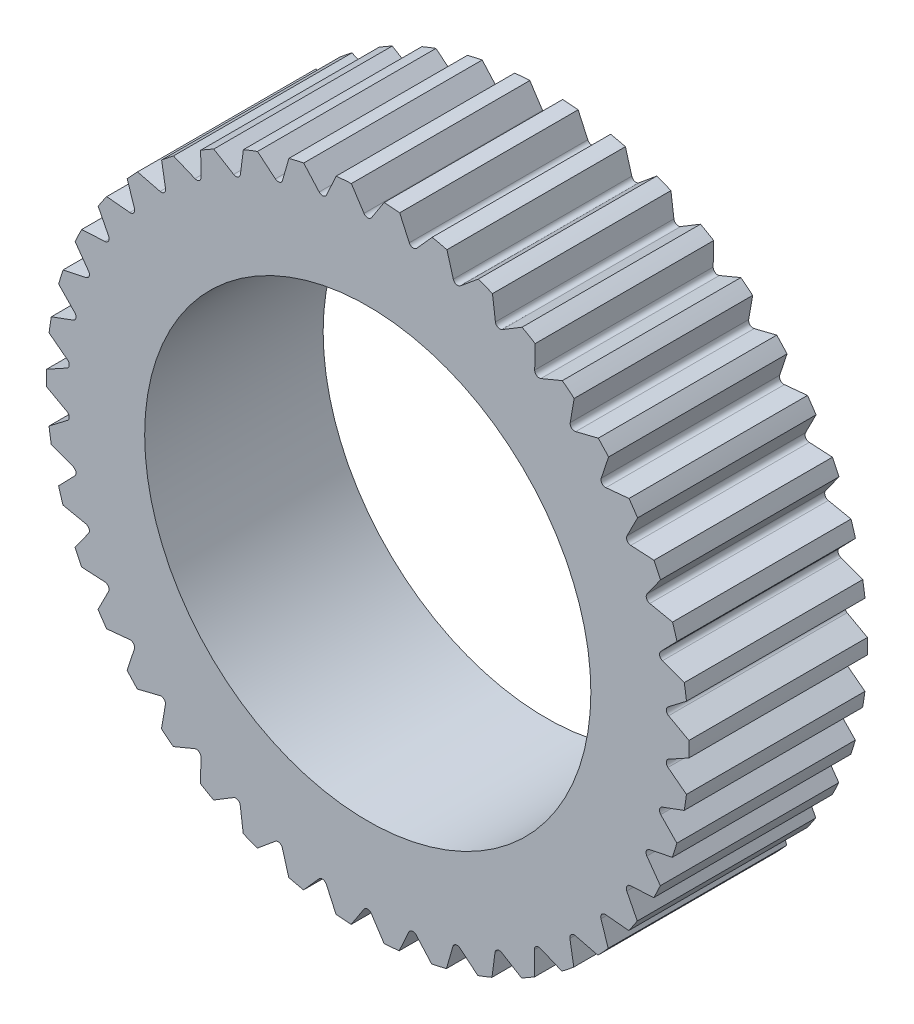
SolidWorks part; units mm, degrees
ref_plane "Front Plane" through (0, 0, 0) normal (0, 0, 1) x (1, 0, 0)
ref_plane "Top Plane" through (0, 0, 0) normal (0, 1, 0) x (1, 0, 0)
ref_plane "Right Plane" through (0, 0, 0) normal (1, 0, 0) x (0, 0, -1)
sketch "Sketch1" plane through (0, 0, 0) normal (0, 0, 1) x (1, 0, 0)
  circle A0 centre (0, 0) radius 3.6
  circle A1 centre (0, 0) radius 2.5
extrude "Boss-Extrude1" add sketch "Sketch1" along normal blind 2
sketch "Sketch2" plane through (0, 0, 2) normal (0, 0, 1) x (1, 0, 0)
  line L0 (0, 0) -> (0, 3.6) construction
  line L1 (0.1277, 3.5089) -> (0.1332, 3.5173)
  line L2 (0.0419, 3.3773) -> (0.1277, 3.5089)
  line L3 (0.2437, 3.6867) -> (-0.2063, 3.6294)
  line L4 (-0.2063, 3.6294) -> (-0.1332, 3.5173)
  line L5 (-0.1277, 3.5089) -> (-0.1332, 3.5173)
  line L7 (-0.1277, 3.5089) -> (-0.0419, 3.3773)
  line L8 (0.1332, 3.5173) -> (0.2437, 3.6867)
  circle A0 centre (0, 0) radius 3.35 construction
  circle A1 centre (0, 0) radius 3.6 construction
  arc A2 (0.0419, 3.3773) -> (-0.0419, 3.3773) centre (0, 3.4046) cw
  point P12 (0, 3.35)
  dimension "D1" = 0.05
extrude "Cut-Extrude5" cut sketch "Sketch2" against normal blind 2
pattern_circular "CirPattern1" count 42 every 8.57 about axis through (0, 0, 0) along (0, 0, 1) of "Cut-Extrude5"
